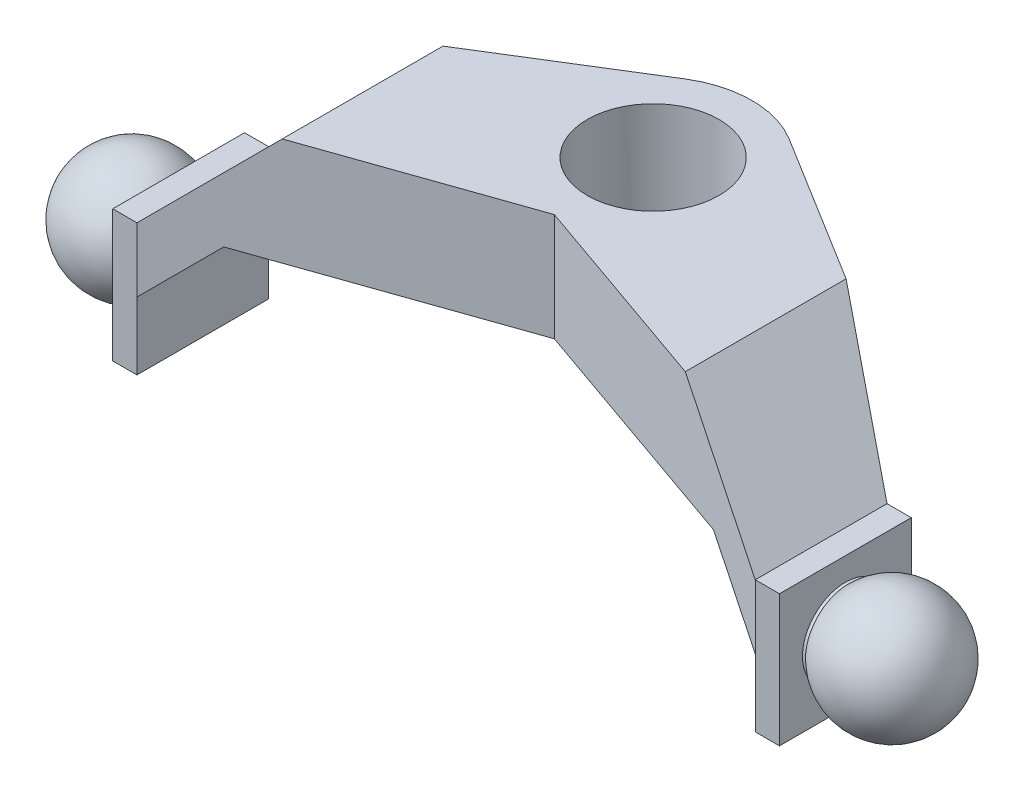
SolidWorks part; units mm, degrees
ref_plane "Front Plane" through (0, 0, 0) normal (0, 0, 1) x (1, 0, 0)
ref_plane "Top Plane" through (0, 0, 0) normal (0, 1, 0) x (1, 0, 0)
ref_plane "Right Plane" through (0, 0, 0) normal (1, 0, 0) x (0, 0, -1)
sketch "Sketch1" plane through (0, 0, 0) normal (0, 1, 0) x (1, 0, 0)
  line L0 (0, 3.81) -> (0, -3.81) construction
  line L1 (-10, 3.81) -> (10, 3.81) construction
  line L2 (-10, 3.81) -> (-10, -3.81) construction
  line L3 (-10, -3.81) -> (10, -3.81) construction
  line L4 (10, 3.81) -> (10, -3.81) construction
  line L5 (-2.0065, 3.2388) -> (-11.9174, -2.9011)
  line L6 (2.0065, 3.2388) -> (11.9174, -2.9011)
  line L7 (-11.9174, -2.9011) -> (-16.9974, -2.9011)
  line L8 (-16.9974, -2.9011) -> (-16.9974, -7.9811)
  line L9 (-16.9974, -7.9811) -> (-11.9174, -7.9811)
  line L10 (-11.9174, -7.9811) -> (0, -3.81)
  line L11 (0, -3.81) -> (11.9174, -7.9811)
  line L12 (11.9174, -7.9811) -> (16.9974, -7.9811)
  line L13 (16.9974, -7.9811) -> (16.9974, -2.9011)
  line L14 (16.9974, -2.9011) -> (11.9174, -2.9011)
  line L15 (-11.9174, -2.9011) -> (-11.9174, -7.9811) construction
  line L16 (11.9174, -2.9011) -> (11.9174, -7.9811) construction
  line L17 (-16.9974, -5.4411) -> (16.9974, -5.4411) construction
  circle A0 centre (0, 0) radius 2.54
  arc A1 (-2.0065, 3.2388) -> (2.0065, 3.2388) centre (0, 0) cw
  dimension "D3" = 5.08
  dimension "D6" = 3.81
  dimension "D1" = 20
  dimension "D2" = 7.62
  dimension "D8" = 5.08
  dimension "D9" = 5.08
extrude "Boss-Extrude1" add sketch "Sketch1" along normal blind 5.08 and the other way blind 5.08
sketch "Sketch2" plane through (0, 0, 0) normal (0, 0, 1) x (1, 0, 0)
  line L0 (-11.9174, -6.5253) -> (-11.9174, -2.4783)
  line L1 (0, 7.5717) -> (0, -8.0181) construction
  line L2 (11.9174, -2.4783) -> (11.9174, -6.5253)
  line L3 (-11.9174, -4.5018) -> (11.9174, -4.5018) construction
  line L4 (-11.9174, -2.4783) -> (-9.4391, 0)
  line L5 (-11.9174, 0) -> (0, 0) construction
  line L6 (-9.4391, 0) -> (9.4391, 0)
  line L7 (0, 0) -> (11.9174, 0) construction
  line L8 (9.4391, 0) -> (11.9174, -2.4783)
  line L9 (-11.9174, -6.5253) -> (11.9174, -6.5253)
  line L10 (-18.0935, 0) -> (-11.9174, 0)
  line L11 (-16.9974, 0) -> (16.9974, 0) construction
  line L12 (-11.9174, 0) -> (-7.7695, 4.1479)
  line L13 (-7.7695, 4.1479) -> (7.7695, 4.1479)
  line L14 (7.7695, 4.1479) -> (11.9174, 0)
  line L15 (16.9974, 0) -> (11.9174, 0) construction
  line L16 (11.9174, 0) -> (18.1185, 0)
  line L17 (18.1185, 0) -> (18.1185, 7.5717)
  line L18 (18.1185, 7.5717) -> (-18.0935, 7.5717)
  line L19 (-18.0935, 7.5717) -> (-18.0935, 0)
  line L21 (-11.9174, -5.08) -> (-11.9174, 5.08) construction
  line L22 (11.9174, -5.08) -> (11.9174, 5.08) construction
  dimension "D1" = 45
  dimension "D2" = 45
extrude "Cut-Extrude1" cut sketch "Sketch2" against normal through all and the other way through all
ref_plane "Plane1" through (0, 0, 5.4411) normal (0, 0, 1) x (1, 0, 0)
sketch "Sketch3" plane through (0, 0, 5.4411) normal (0, 0, 1) x (1, 0, 0)
  line L0 (-16.9974, -2.54) -> (16.9974, -2.54) construction
  line L1 (-16.9974, -5.08) -> (-16.9974, 0) construction
  line L2 (16.9974, -5.08) -> (16.9974, 0) construction
  line L3 (0, 8.5027) -> (0, -6.1929) construction
  line L4 (-12.9676, -0.8858) -> (-12.8512, -0.8858)
  line L5 (-12.8512, 1.8011) -> (-18.1583, 1.8011)
  line L6 (-18.1583, 1.8011) -> (-18.1583, -2.54)
  line L7 (-16.9974, -2.54) -> (-16.9974, -0.2798) construction
  line L8 (-18.1583, -2.54) -> (-16.9974, -2.54)
  line L9 (-12.8512, -0.8858) -> (-12.8512, 1.8011)
  line L10 (12.8512, -0.8858) -> (12.8512, 1.8011)
  line L11 (18.1583, -2.54) -> (16.9974, -2.54)
  line L12 (18.1583, 1.8011) -> (18.1583, -2.54)
  line L13 (12.8512, 1.8011) -> (18.1583, 1.8011)
  line L14 (12.9676, -0.8858) -> (12.8512, -0.8858)
  arc A0 (-12.9676, -0.8858) -> (-16.9974, -2.54) centre (-14.643, -2.54) ccw
  arc A1 (12.9676, -0.8858) -> (16.9974, -2.54) centre (14.643, -2.54) cw
revolve "Cut-Revolve1" cut sketch "Sketch3" angle 360 about L0
